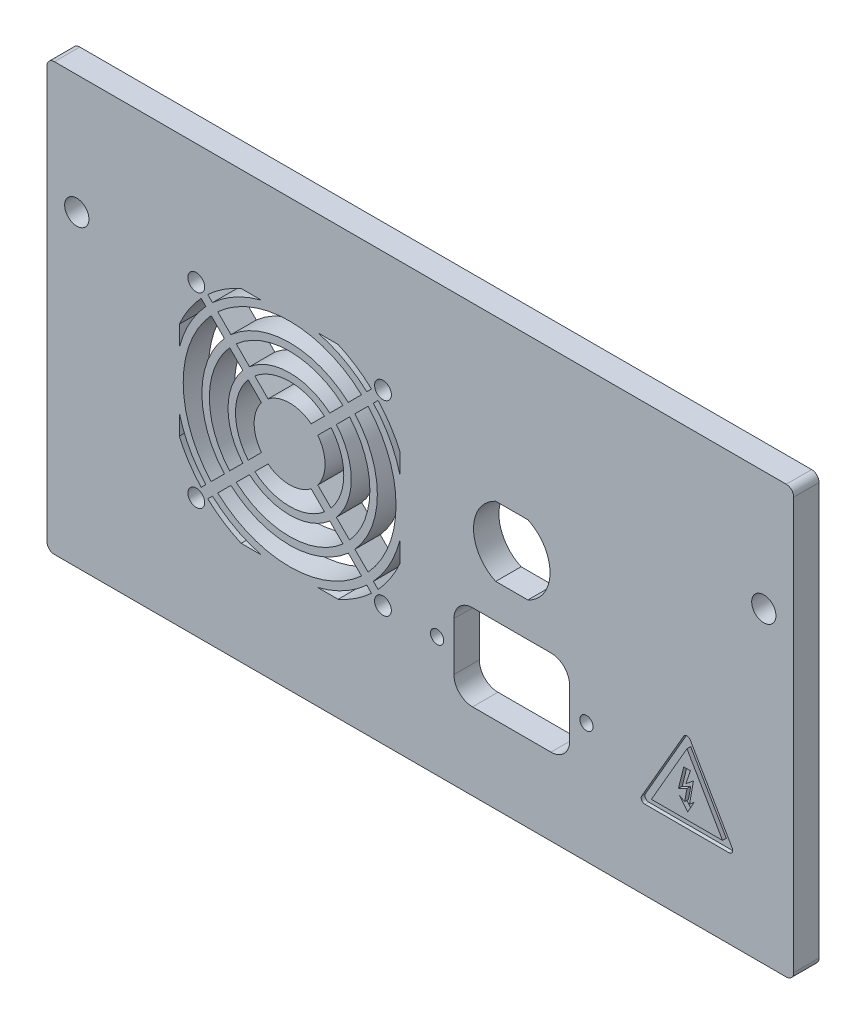
SolidWorks part; units mm, degrees
ref_plane "Front Plane" through (0, 0, 0) normal (0, 0, 1) x (1, 0, 0)
ref_plane "Top Plane" through (0, 0, 0) normal (0, 1, 0) x (1, 0, 0)
ref_plane "Right Plane" through (0, 0, 0) normal (1, 0, 0) x (0, 0, -1)
sketch "Sketch1" plane through (0, 0, 0) normal (0, 0, 1) x (1, 0, 0)
  line L1 (100, -57.15) -> (-100, -57.15)
  line L2 (100, -57.15) -> (100, 57.15)
  line L3 (100, 57.15) -> (-100, 57.15)
  line L4 (-100, -57.15) -> (-100, 57.15)
  line L5 (100, -57.15) -> (-100, 57.15) construction
  line L6 (100, 57.15) -> (-100, -57.15) construction
  point P0 (0, 0)
  dimension "D1" = 200
  dimension "D2" = 114.3
extrude "Boss-Extrude1" add sketch "Sketch1" along normal blind 6.8
sketch "Sketch2" plane through (0, 0, 6.8) normal (0, 0, 1) x (1, 0, 0)
  line L0 (100, 57.15) -> (-100, 57.15) construction
  line L1 (92, 25.25) -> (-92, 25.25) construction
  circle A0 centre (-92, 25.25) radius 3.25
  circle A1 centre (92, 25.25) radius 3.25
  point P10 (0, 25.25)
  dimension "D1" = 6.5
  dimension "D2" = 92
  dimension "D3" = 31.9
extrude "Cut-Extrude1" cut sketch "Sketch2" against normal blind 6.8
fillet "Fillet1" radius 2 4 edges at (100, 57.15, 3.4) (100, -57.15, 3.4) (-100, -57.15, 3.4) (-100, 57.15, 3.4)
sketch "Sketch3" plane through (0, 0, 6.8) normal (0, 0, 1) x (1, 0, 0)
  line L0 (44.5, -25) -> (40, -25) construction
  line L1 (9, -13.5) -> (40, -13.5)
  line L2 (9, -13.5) -> (9, -36.5)
  line L3 (9, -36.5) -> (40, -36.5)
  line L4 (40, -13.5) -> (40, -36.5)
  line L5 (9, -13.5) -> (40, -36.5) construction
  line L6 (9, -36.5) -> (40, -13.5) construction
  line L7 (9, -25) -> (4.5, -25) construction
  line L8 (20.1904, 14.3) -> (28.8096, 14.3)
  line L9 (28.8096, -4.3) -> (20.1904, -4.3)
  line L10 (24.5, 14.3) -> (24.5, 5) construction
  line L11 (24.5, 5) -> (24.5, -4.3) construction
  line L12 (100, -55.15) -> (100, 55.15) construction
  circle A2 centre (4.5, -25) radius 1.775
  circle A3 centre (44.5, -25) radius 1.775
  arc A4 (28.8096, -4.3) -> (28.8096, 14.3) centre (24.5, 5) ccw
  arc A5 (20.1904, 14.3) -> (20.1904, -4.3) centre (24.5, 5) ccw
  point P0 (24.5, -25)
  dimension "D3" = 3.55
  dimension "D7" = 20.5
  dimension "D1" = 23
  dimension "D2" = 31
  dimension "D4" = 20
  dimension "D5" = 5
  dimension "D6" = 25
  dimension "D8" = 18.6
  dimension "D9" = 60
extrude "Cut-Extrude2" cut sketch "Sketch3" against normal up to vertex (6.8 mm away) up to point (0, 0, 0)
fillet "Fillet2" radius 5 4 edges at (40, -36.5, 3.4) (9, -36.5, 3.4) (9, -13.5, 3.4) (40, -13.5, 3.4)
sketch "Sketch6" plane through (0, 0, 6.8) normal (0, 0, 1) x (1, 0, 0)
  line L0 (80.9479, -34) -> (71.4216, -17.5)
  line L1 (70.5556, -15) -> (59.2972, -34.5)
  line L2 (60.1633, -36) -> (82.6799, -36)
  line L3 (83.5459, -34.5) -> (72.2876, -15)
  line L4 (71.4216, -17.5) -> (61.8953, -34)
  line L5 (61.8953, -34) -> (80.9479, -34)
  line L8 (70.551, -22.1493) -> (72.3474, -22.1493)
  line L9 (72.3474, -22.1493) -> (71.1071, -25.7647)
  line L10 (71.1071, -25.7647) -> (73.151, -24.1098)
  line L11 (73.151, -24.1098) -> (72.1078, -29.9839)
  line L12 (72.1078, -29.9839) -> (73.3464, -28.9811)
  line L13 (73.3464, -28.9811) -> (71.6268, -32.0315)
  line L14 (71.6268, -32.0315) -> (69.4232, -29.31)
  line L15 (69.4232, -29.31) -> (70.8114, -30.0926)
  line L16 (70.8114, -30.0926) -> (71.4216, -26.7094)
  line L17 (71.4216, -26.7094) -> (69.1426, -27.8405)
  line L18 (69.1426, -27.8405) -> (70.551, -22.1493)
  arc A1 (83.5459, -34.5) -> (82.6799, -36) centre (82.6799, -35) cw
  arc A2 (60.1633, -36) -> (59.2972, -34.5) centre (60.1633, -35) cw
  arc A3 (72.2876, -15) -> (70.5556, -15) centre (71.4216, -15.5) ccw
sketch "Sketch7" plane through (0, 0, 6.8) normal (0, 0, 1) x (1, 0, 0)
  line L1 (32.8044, 35.7017) -> (29.4221, 29.8433)
  line L2 (29.4221, 29.8433) -> (36.1867, 29.8433)
  line L3 (36.1867, 29.8433) -> (32.8044, 35.7017)
  line L4 (32.8044, 36.7996) -> (28.4712, 29.2943)
  line L5 (28.4712, 29.2943) -> (37.1376, 29.2943)
  line L6 (37.1376, 29.2943) -> (32.8044, 36.7996)
  circle A0 centre (32.8044, 31.7961) radius 1.9528 construction
  circle A1 centre (32.8044, 31.7961) radius 2.5018 construction
  text T0 "Risk of Electrical Shock.\r\nDisconnect power cord from\r\nelectrical outlet before \r\nremoving this panel or\r\nstarting any service" font "Century Gothic" height 3
  text T1 "WARNING" font "Century Gothic" height 6
  text T2 "!"
extrude "Cut-Extrude5" [suppressed] cut sketch "Sketch7" against normal blind 1
sketch "Sketch4" plane through (0, 0, 6.8) normal (0, 0, 1) x (1, 0, 0)
  line L0 (-64.55, 12.9909) -> (-64.55, -12.9909)
  line L1 (-47.9909, -29.55) -> (-22.0091, -29.55)
  line L2 (-5.45, -12.9909) -> (-5.45, 12.9909)
  line L3 (-22.0091, 29.55) -> (-47.9909, 29.55)
  line L5 (-10, -25) -> (-60, -25) construction
  line L6 (-10, -25) -> (-10, 25) construction
  line L7 (-10, 25) -> (-60, 25) construction
  line L8 (-60, -25) -> (-60, 25) construction
  line L9 (-10, -25) -> (-60, 25) construction
  line L10 (-10, 25) -> (-60, -25) construction
  circle A4 centre (-10, 25) radius 2.25
  circle A5 centre (-60, 25) radius 2.25
  circle A6 centre (-60, -25) radius 2.25
  circle A7 centre (-10, -25) radius 2.25
  arc A10 (-5.45, 12.9909) -> (-22.0091, 29.55) centre (-35, 0) ccw
  arc A11 (-47.9909, 29.55) -> (-64.55, 12.9909) centre (-35, 0) ccw
  arc A14 (-64.55, -12.9909) -> (-47.9909, -29.55) centre (-35, 0) ccw
  arc A15 (-22.0091, -29.55) -> (-5.45, -12.9909) centre (-35, 0) ccw
  circle A17 centre (-35, 0) radius 7.5
  circle A19 centre (-35, 0) radius 9.5
  circle A20 centre (-35, 0) radius 14.5
  circle A21 centre (-35, 0) radius 16.5
  circle A22 centre (-35, 0) radius 21.5
  circle A23 centre (-35, 0) radius 23.5
  circle A24 centre (-35, 0) radius 28.5
  arc A25 (-42.553, 29.55) -> (-64.55, 7.553) centre (-35, 0) ccw
  arc A27 (-64.55, -7.553) -> (-42.553, -29.55) centre (-35, 0) ccw
  arc A28 (-27.447, -29.55) -> (-5.45, -7.553) centre (-35, 0) ccw
  arc A29 (-5.45, 7.553) -> (-27.447, 29.55) centre (-35, 0) ccw
  dimension "D1" = 35
  dimension "D9" = 15
extrude "Cut-Extrude3" cut sketch "Sketch4" against normal through all contours A20 A19 | A22 A21 | A24 A23 | A29 L2 A10 L3 | A25 L3 A11 L0 | A27 L0 A14 L1 | A28 L1 A15 L2 | A7 | A6 | A5 | A4
sketch "Sketch9" plane through (0, 0, 6.8) normal (0, 0, 1) x (1, 0, 0)
  line L0 (-10.8436, 22.3886) -> (-57.3886, -24.1564)
  line L1 (-33.75, -33.3586) -> (-36.25, -33.3586)
  line L2 (-33.75, -33.3586) -> (-33.75, 33.3586)
  line L3 (-33.75, 33.3586) -> (-36.25, 33.3586)
  line L4 (-36.25, -33.3586) -> (-36.25, 33.3586)
  line L5 (-33.75, -33.3586) -> (-36.25, 33.3586) construction
  line L6 (-33.75, 33.3586) -> (-36.25, -33.3586) construction
  line L7 (-73.4567, -1.25) -> (3.4567, -1.25)
  line L8 (-73.4567, -1.25) -> (-73.4567, 1.25)
  line L9 (-73.4567, 1.25) -> (3.4567, 1.25)
  line L10 (3.4567, -1.25) -> (3.4567, 1.25)
  line L11 (-73.4567, -1.25) -> (3.4567, 1.25) construction
  line L12 (-73.4567, 1.25) -> (3.4567, -1.25) construction
  line L13 (-10.8436, 22.3886) -> (-12.6114, 24.1564)
  line L14 (-57.3886, -24.1564) -> (-59.1564, -22.3886)
  line L15 (-12.6114, 24.1564) -> (-59.1564, -22.3886)
  line L16 (-10.8436, 22.3886) -> (-59.1564, -22.3886) construction
  line L17 (-57.3886, -24.1564) -> (-12.6114, 24.1564) construction
  line L18 (-57.3084, 24.0762) -> (-10.9238, -22.3084)
  line L19 (-57.3084, 24.0762) -> (-59.0762, 22.3084)
  line L20 (-10.9238, -22.3084) -> (-12.6916, -24.0762)
  line L21 (-59.0762, 22.3084) -> (-12.6916, -24.0762)
  line L22 (-57.3084, 24.0762) -> (-12.6916, -24.0762) construction
  line L23 (-10.9238, -22.3084) -> (-59.0762, 22.3084) construction
  point P0 (-35, 0)
  point P6 (-35, 0)
  point P12 (-35, 0)
  point P13 (-35, 0)
  arc M55 (-5.45, 7.553) -> (-27.447, 29.55) centre (-35, 0) ccw
  arc M57 (-22.0091, 29.55) -> (-5.45, 12.9909) centre (-35, 0) cw
  arc M59 (-42.553, 29.55) -> (-64.55, 7.553) centre (-35, 0) ccw
  arc M61 (-64.55, 12.9909) -> (-47.9909, 29.55) centre (-35, 0) cw
  arc M63 (-64.55, -7.553) -> (-42.553, -29.55) centre (-35, 0) ccw
  arc M65 (-47.9909, -29.55) -> (-64.55, -12.9909) centre (-35, 0) cw
  arc M67 (-27.447, -29.55) -> (-5.45, -7.553) centre (-35, 0) ccw
  arc M69 (-5.45, -12.9909) -> (-22.0091, -29.55) centre (-35, 0) cw
  dimension "D1" = 2.5
  dimension "D2" = 2.5
  dimension "D3" = 2.5
  dimension "D4" = 45
  dimension "D5" = 45
extrude "Boss-Extrude7" add sketch "Sketch9" against normal up to surface (6.8 mm away) contours L4 L9 L2 L3 | L7 L10 L9 L2 | L9 L8 L7 L4 | L7 L4 L1 L2 | L2 L21 L20 L18 L7 | L7 L15 L14 L0 L4 | L13 L15 L2 L9 L0 | L19 L21 L9 L4 L18 | L15 L0 M57 M55 | L21 L18 M61 M59 | L15 L0 M63 M65 | L21 L18 M67 M69
sketch "Sketch10" [suppressed] plane through (0, 0, 6.8) normal (0, 0, 1) x (1, 0, 0)
  line L0 (100, -55.15) -> (100, 55.15) construction
  line L1 (85, 18.05) -> (15.15, 18.05)
  line L2 (85, 18.05) -> (85, 56.15)
  line L3 (85, 56.15) -> (15.15, 56.15)
  line L4 (15.15, 18.05) -> (15.15, 56.15)
  line L5 (98, 57.15) -> (-98, 57.15) construction
  dimension "D1" = 69.85
  dimension "D2" = 38.1
  dimension "D3" = 1
  dimension "D4" = 15
extrude "Cut-Extrude6" cut sketch "Sketch6" against normal blind 1 contours L3 A3 L1 A2 L2 A1 L5 L4 L0 | L18 L17 L16 L15 L14 L13 L12 L11 L10 L9 L8
